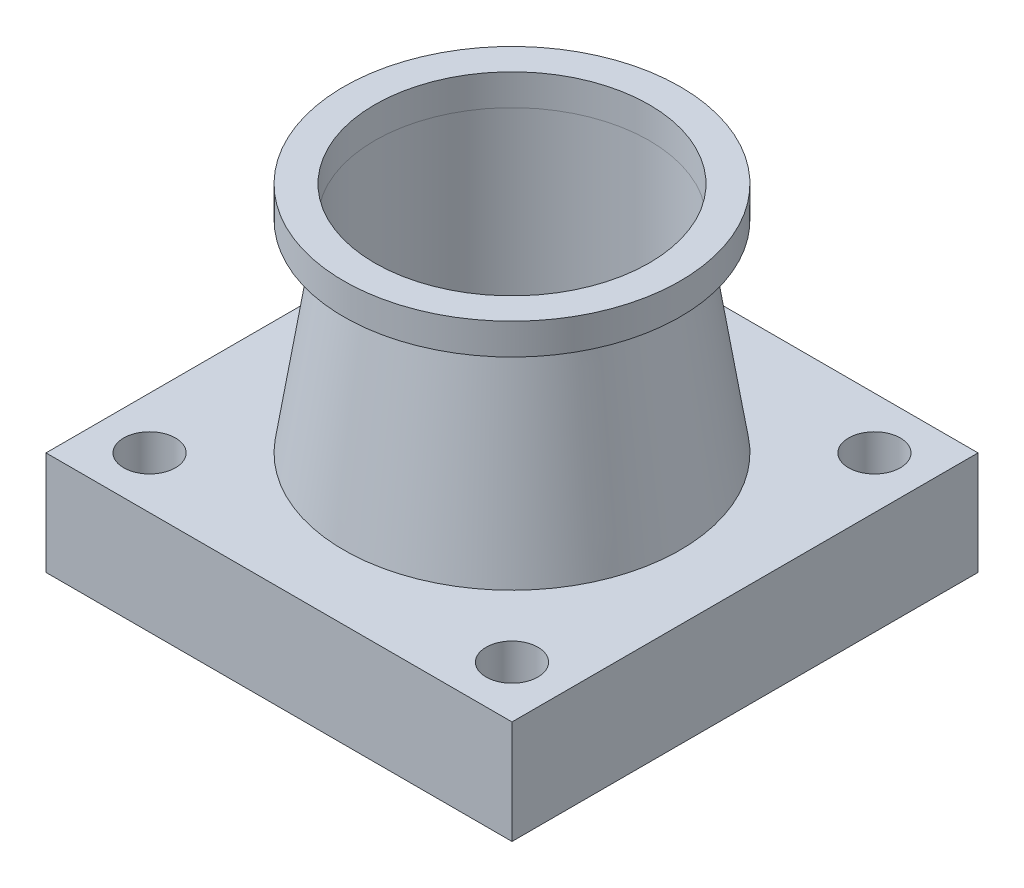
SolidWorks part; units mm, degrees
ref_plane "Front Plane" through (0, 0, 0) normal (0, 0, 1) x (1, 0, 0)
ref_plane "Top Plane" through (0, 0, 0) normal (0, 1, 0) x (1, 0, 0)
ref_plane "Right Plane" through (0, 0, 0) normal (1, 0, 0) x (0, 0, -1)
sketch "Sketch1" plane through (0, 0, 0) normal (0, 1, 0) x (1, 0, 0)
  line L1 (-45, -45) -> (45, -45)
  line L2 (-45, -45) -> (-45, 45)
  line L3 (-45, 45) -> (45, 45)
  line L4 (45, -45) -> (45, 45)
  line L5 (-45, -45) -> (45, 45) construction
  line L6 (-45, 45) -> (45, -45) construction
  point P0 (0, 0)
  dimension "D1" = 90
  dimension "D2" = 90
extrude "Boss-Extrude1" add sketch "Sketch1" along normal blind 20
sketch "Sketch2" plane through (0, 0, 0) normal (1, 0, 0) x (0, 0, -1)
  line L0 (0, 20) -> (0, 65)
  line L1 (-45, 20) -> (45, 20) construction
  line L2 (0, 65) -> (32.5, 65)
  line L3 (32.5, 65) -> (32.5, 59)
  line L4 (32.5, 59) -> (26.5, 59)
  line L5 (26.5, 59) -> (32.5, 20)
  line L6 (32.5, 20) -> (0, 20)
  line L7 (0, 20) -> (0, 103.4123) construction
  dimension "D1" = 32.5
  dimension "D2" = 32.5
  dimension "D3" = 26.5
  dimension "D4" = 45
  dimension "D5" = 6
revolve "Revolve1" add sketch "Sketch2" angle 360 about L7
sketch "Sketch3" plane through (0, 65, 0) normal (0, 1, 0) x (1, 0, 0)
  circle A0 centre (0, 0) radius 26.5
  dimension "D1" = 53
extrude "Cut-Extrude1" cut sketch "Sketch3" against normal up to surface (45 mm away) up to face at (0, 20, -32.5)
sketch "Sketch4" plane through (0, 20, 0) normal (0, 1, 0) x (1, 0, 0)
  line L0 (-45, -45) -> (45, -45) construction
  line L1 (-45, 45) -> (-45, -45) construction
  line L2 (45, -45) -> (45, 45) construction
  line L3 (45, 45) -> (-45, 45) construction
  circle A0 centre (-35, -35) radius 5
  circle A1 centre (35, -35) radius 5
  circle A2 centre (35, 35) radius 5
  circle A3 centre (-35, 35) radius 5
  dimension "D1" = 10
  dimension "D2" = 10
  dimension "D3" = 10
  dimension "D4" = 10
  dimension "D5" = 10
  dimension "D6" = 10
  dimension "D7" = 10
  dimension "D8" = 10
  dimension "D9" = 10
extrude "Cut-Extrude2" cut sketch "Sketch4" against normal through all
